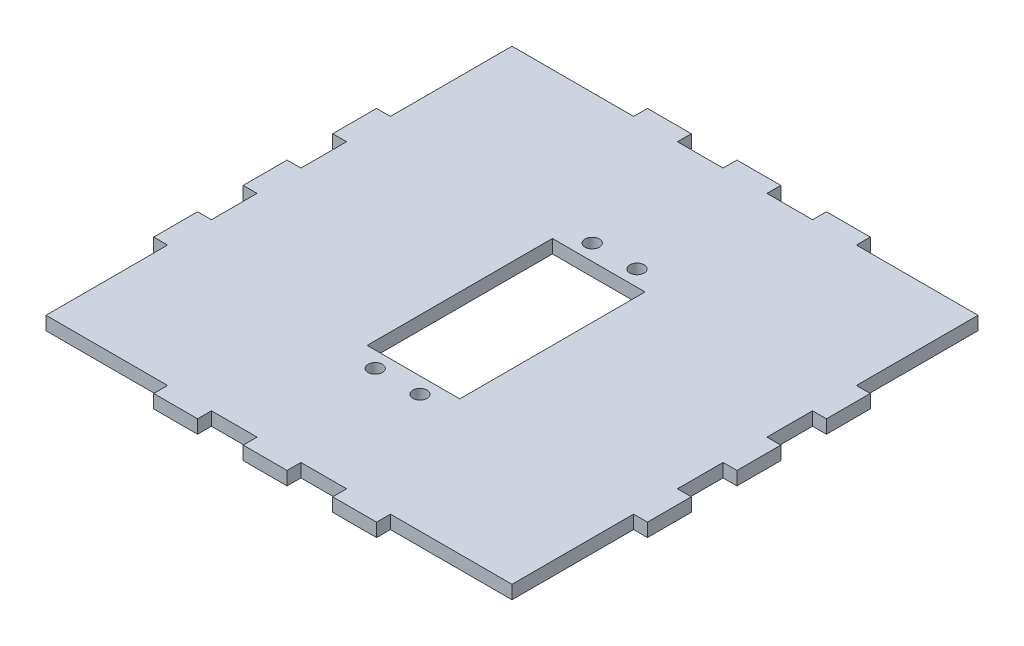
SolidWorks part; units mm, degrees
ref_plane "Front Plane" through (0, 0, 0) normal (0, 0, 1) x (1, 0, 0)
ref_plane "Top Plane" through (0, 0, 0) normal (0, 1, 0) x (1, 0, 0)
ref_plane "Right Plane" through (0, 0, 0) normal (1, 0, 0) x (0, 0, -1)
sketch "Sketch1" plane through (0, 0, 0) normal (0, 1, 0) x (1, 0, 0)
  line L0 (0, 0) -> (0, 21) construction
  line L1 (-55.1722, 66.843) -> (-55.1722, -43.5014) construction
  line L2 (55.1722, -43.5014) -> (-55.1722, -43.5014) construction
  line L3 (55.1722, -43.5014) -> (55.1722, 66.843) construction
  line L4 (55.1722, 66.843) -> (-55.1722, 66.843) construction
  line L5 (-55.1722, 66.843) -> (-55.1722, -43.5014)
  line L6 (55.1722, -43.5014) -> (-55.1722, -43.5014)
  line L7 (55.1722, -43.5014) -> (55.1722, 66.843)
  line L8 (55.1722, 66.843) -> (-55.1722, 66.843)
  line L9 (10.05, 30.75) -> (-10.05, 30.75) construction
  line L10 (-10.05, 30.75) -> (-10.05, -10.05) construction
  line L11 (10.05, -10.05) -> (-10.05, -10.05) construction
  line L12 (10.05, 30.75) -> (10.05, -10.05) construction
  line L13 (10.05, 30.75) -> (-10.05, 30.75) construction
  line L14 (-10.05, 30.75) -> (-10.05, -10.05) construction
  line L15 (10.05, -10.05) -> (-10.05, -10.05) construction
  line L16 (10.05, 30.75) -> (10.05, -10.05) construction
  line L17 (10.35, 31.05) -> (-10.35, 31.05)
  line L18 (-10.35, 31.05) -> (-10.35, -10.35)
  line L19 (10.35, -10.35) -> (-10.35, -10.35)
  line L20 (10.35, 31.05) -> (10.35, -10.35)
  circle A0 centre (0, 0) radius 21 construction
  circle A1 centre (0, 0) radius 21 construction
  circle A2 centre (5, 34.6) radius 2 construction
  circle A3 centre (-5, 34.6) radius 2 construction
  circle A4 centre (-5, -13.9) radius 2 construction
  circle A5 centre (5, -13.9) radius 2 construction
  circle A6 centre (5, 34.6) radius 2 construction
  circle A7 centre (-5, 34.6) radius 2 construction
  circle A8 centre (-5, -13.9) radius 2 construction
  circle A9 centre (5, -13.9) radius 2 construction
  circle A10 centre (-5, 34.6) radius 1.6
  circle A11 centre (5, 34.6) radius 1.6
  circle A12 centre (5, -13.9) radius 1.6
  circle A13 centre (-5, -13.9) radius 1.6
  dimension "D2" = 3.2
  dimension "D1" = 0.3
extrude "Boss-Extrude1" add sketch "Sketch1" along normal up to vertex (3 mm away)
sketch "Sketch2" plane through (0, 0, 0) normal (0, 1, 0) x (1, 0, 0)
  line L0 (-55.1722, 66.843) -> (-55.1722, -43.5014) construction
  line L1 (55.1722, -43.5014) -> (-55.1722, -43.5014) construction
  line L2 (55.1722, -43.5014) -> (55.1722, 66.843) construction
  line L3 (55.1722, 66.843) -> (-55.1722, 66.843) construction
  line L4 (-52.1722, -43.5014) -> (-52.1722, 63.843) construction
  line L5 (52.1722, 63.843) -> (-52.1722, 63.843) construction
  line L6 (52.1722, 63.843) -> (52.1722, -43.5014) construction
  line L7 (-55.1722, -40.5014) -> (55.1722, -40.5014) construction
  line L8 (-55.1722, 66.843) -> (-55.1722, -43.5014) construction
  line L9 (55.1722, -43.5014) -> (-55.1722, -43.5014) construction
  line L10 (55.1722, -43.5014) -> (55.1722, 66.843) construction
  line L11 (55.1722, 66.843) -> (-55.1722, 66.843) construction
  line L12 (-52.1722, -40.5014) -> (-52.1722, 63.843) construction
  line L13 (52.1722, 63.843) -> (-52.1722, 63.843) construction
  line L14 (52.1722, 63.843) -> (52.1722, -40.5014) construction
  line L15 (-52.1722, -40.5014) -> (52.1722, -40.5014) construction
  line L16 (-55.1722, 16.6708) -> (-52.1722, 16.6708) construction
  line L17 (-55.1722, 26.6708) -> (-52.1722, 26.6708) construction
  line L18 (-55.1722, 36.6708) -> (-52.1722, 36.6708) construction
  line L19 (0, -40.5014) -> (0, 63.843) construction
  line L20 (0, 11.6708) -> (-52.1722, 11.6708) construction
  line L22 (25, 66.843) -> (25, 63.843) construction
  line L23 (15, 66.843) -> (15, 63.843) construction
  line L24 (-55.1722, 6.6708) -> (-52.1722, 6.6708) construction
  line L25 (5, 66.843) -> (5, 63.843) construction
sketch "Sketch3" plane through (0, 0, 0) normal (0, 1, 0) x (1, 0, 0)
  line L0 (0, 11.6708) -> (-52.1722, 11.6708) construction
  line L1 (15.1, 66.943) -> (4.9, 66.943)
  line L2 (15.1, 66.943) -> (15.1, 63.743)
  line L3 (15.1, 63.743) -> (4.9, 63.743)
  line L4 (4.9, 66.943) -> (4.9, 63.743)
  line L5 (24.9, 66.943) -> (55.2722, 66.943)
  line L6 (24.9, 66.943) -> (24.9, 63.743)
  line L7 (24.9, 63.743) -> (52.0722, 63.743)
  line L8 (52.0722, -40.4014) -> (52.0722, -40.5014) construction
  line L9 (55.2722, 36.5708) -> (52.0722, 36.5708)
  line L10 (55.2722, 36.5708) -> (55.2722, 66.943)
  line L11 (55.1722, -43.6014) -> (55.1722, -43.5014) construction
  line L12 (52.0722, 36.5708) -> (52.0722, 63.743)
  line L13 (55.2722, 26.7708) -> (52.0722, 26.7708)
  line L14 (55.2722, 26.7708) -> (55.2722, 16.5708)
  line L15 (55.2722, 16.5708) -> (52.0722, 16.5708)
  line L16 (52.0722, 26.7708) -> (52.0722, 16.5708)
  line L17 (-53.6722, 36.5708) -> (-53.6722, 36.6708) construction
  line L18 (55.1722, -43.5014) -> (-55.1722, -43.5014) construction
  line L19 (24.9, -40.4014) -> (52.0722, -40.4014)
  line L20 (24.9, -40.4014) -> (24.9, -43.6014)
  line L21 (0, 11.6708) -> (0, -43.5014) construction
  line L22 (25, -40.5014) -> (24.9, -40.5014) construction
  line L23 (-55.1722, 36.6708) -> (-52.1722, 36.6708) construction
  line L24 (5.1, 66.843) -> (5, 66.843) construction
  line L25 (52.0722, -40.4014) -> (52.0722, -13.2292)
  line L26 (-55.1722, 26.6708) -> (-52.1722, 26.6708) construction
  line L27 (53.6722, 16.5708) -> (53.6722, 16.6708) construction
  line L28 (24.9, -43.6014) -> (55.2722, -43.6014)
  line L29 (55.2722, -13.2292) -> (55.2722, -43.6014)
  line L30 (52.0722, -13.2292) -> (55.2722, -13.2292)
  line L31 (-52.1722, -40.5014) -> (52.1722, -40.5014) construction
  line L32 (52.0722, -26.8153) -> (52.1722, -26.8153) construction
  line L33 (55.2722, -28.4153) -> (55.1722, -28.4153) construction
  line L34 (55.1722, -43.5014) -> (55.1722, 66.843) construction
  line L35 (52.1722, 63.843) -> (52.1722, -40.5014) construction
  line L36 (53.6722, 36.5708) -> (53.6722, 36.6708) construction
  line L37 (-55.1722, 16.6708) -> (-52.1722, 16.6708) construction
  line L38 (53.6722, 26.7708) -> (53.6722, 26.6708) construction
  line L39 (24.9, 65.343) -> (25, 65.343) construction
  line L40 (55.2722, -3.4292) -> (52.0722, -3.4292)
  line L41 (15.1, 65.343) -> (15, 65.343) construction
  line L42 (4.9, 65.343) -> (5, 65.343) construction
  line L43 (5, 66.843) -> (5, 63.843) construction
  line L44 (15, 66.843) -> (15, 63.843) construction
  line L45 (25, 66.843) -> (25, 63.843) construction
  line L46 (-52.0722, -13.2292) -> (-55.2722, -13.2292)
  line L47 (-52.0722, -40.4014) -> (-52.0722, -13.2292)
  line L48 (-24.9, -40.4014) -> (-52.0722, -40.4014)
  line L49 (-24.9, -40.4014) -> (-24.9, -43.6014)
  line L50 (-24.9, -43.6014) -> (-55.2722, -43.6014)
  line L51 (-55.2722, -13.2292) -> (-55.2722, -43.6014)
  line L52 (-55.2722, 26.7708) -> (-52.0722, 26.7708)
  line L53 (-52.0722, 26.7708) -> (-52.0722, 16.5708)
  line L54 (-55.2722, 16.5708) -> (-52.0722, 16.5708)
  line L55 (-55.2722, 26.7708) -> (-55.2722, 16.5708)
  line L56 (-15.1, 66.943) -> (-15.1, 63.743)
  line L57 (-15.1, 66.943) -> (-4.9, 66.943)
  line L58 (-4.9, 66.943) -> (-4.9, 63.743)
  line L59 (-15.1, 63.743) -> (-4.9, 63.743)
  line L60 (-55.2722, 36.5708) -> (-52.0722, 36.5708)
  line L61 (-52.0722, 36.5708) -> (-52.0722, 63.743)
  line L62 (-24.9, 63.743) -> (-52.0722, 63.743)
  line L63 (-24.9, 66.943) -> (-24.9, 63.743)
  line L64 (-24.9, 66.943) -> (-55.2722, 66.943)
  line L65 (-55.2722, 36.5708) -> (-55.2722, 66.943)
  line L66 (52.0722, -3.4292) -> (52.0722, 6.7708)
  line L67 (55.2722, 6.7708) -> (52.0722, 6.7708)
  line L68 (55.2722, -3.4292) -> (55.2722, 6.7708)
  line L69 (-55.2722, -3.4292) -> (-55.2722, 6.7708)
  line L70 (-55.2722, -3.4292) -> (-52.0722, -3.4292)
  line L71 (-52.0722, -3.4292) -> (-52.0722, 6.7708)
  line L72 (-55.2722, 6.7708) -> (-52.0722, 6.7708)
  line L73 (-15.1, -43.6014) -> (-15.1, -40.4014)
  line L74 (-15.1, -43.6014) -> (-4.9, -43.6014)
  line L75 (-4.9, -43.6014) -> (-4.9, -40.4014)
  line L76 (-15.1, -40.4014) -> (-4.9, -40.4014)
  line L77 (15.1, -43.6014) -> (15.1, -40.4014)
  line L78 (15.1, -43.6014) -> (4.9, -43.6014)
  line L79 (4.9, -43.6014) -> (4.9, -40.4014)
  line L80 (15.1, -40.4014) -> (4.9, -40.4014)
extrude "Cut-Extrude1" cut sketch "Sketch3" along normal through all
